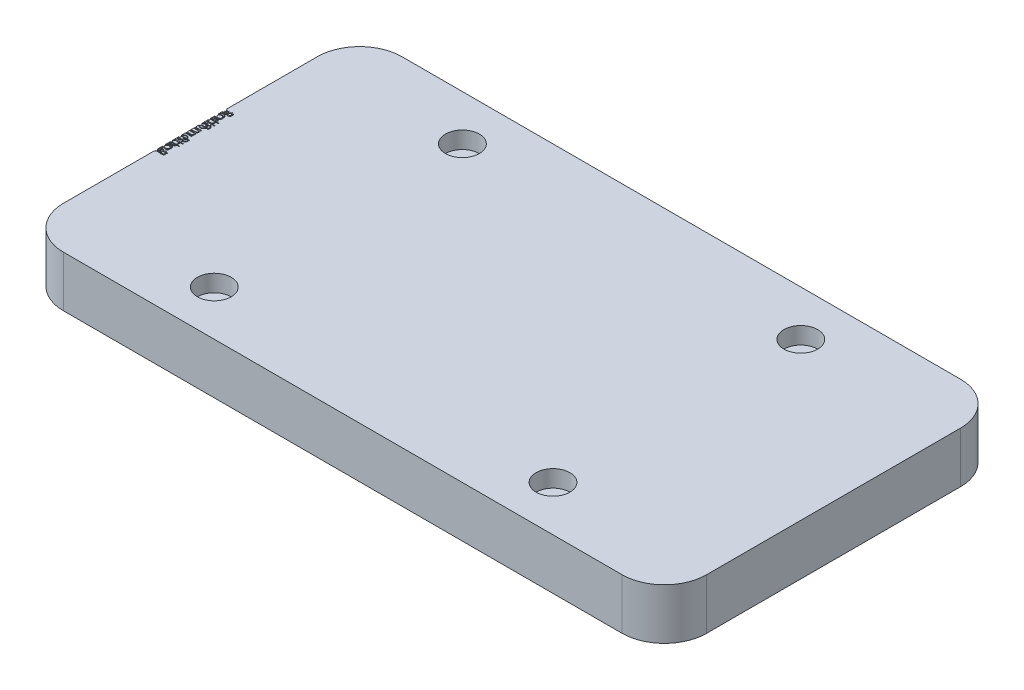
SolidWorks part; units mm, degrees
ref_plane "Front Plane" through (0, 0, 0) normal (0, 0, 1) x (1, 0, 0)
ref_plane "Top Plane" through (0, 0, 0) normal (0, 1, 0) x (1, 0, 0)
ref_plane "Right Plane" through (0, 0, 0) normal (1, 0, 0) x (0, 0, -1)
sketch "Sketch1" plane through (0, 0, 0) normal (0, 1, 0) x (1, 0, 0)
  line L1 (-482.6, 254) -> (482.6, 254)
  line L2 (-482.6, 254) -> (-482.6, -254)
  line L3 (-482.6, -254) -> (482.6, -254)
  line L4 (482.6, 254) -> (482.6, -254)
  line L5 (-482.6, 254) -> (482.6, -254) construction
  line L6 (-482.6, -254) -> (482.6, 254) construction
  point P0 (0, 0)
  dimension "D1" = 508
  dimension "D2" = 965.2
extrude "Boss-Extrude1" add sketch "Sketch1" along normal blind 76.2
fillet "Fillet1" radius 63.5 4 edges at (-482.6, 38.1, -254) (482.6, 38.1, -254) (482.6, 38.1, 254) (-482.6, 38.1, 254)
sketch "Sketch3" plane through (0, 76.2, 0) normal (0, 1, 0) x (1, 0, 0)
  circle A0 centre (-260.576, -186.1285) radius 25.4
  circle A1 centre (247.4239, -185.9218) radius 25.4
  text T0 "Bottom Back" font "Century Gothic" height in points 48
  point P5 (-260.576, -185.9218)
  dimension "D1" = 508
  dimension "D2" = 50.8
  dimension "D3" = 50.8
extrude "Cut-Extrude2" cut sketch "Sketch3" against normal blind 25.4
mirror "Mirror1" about plane through (0, 0, 0) normal (0, 0, 1) of "Cut-Extrude2"
